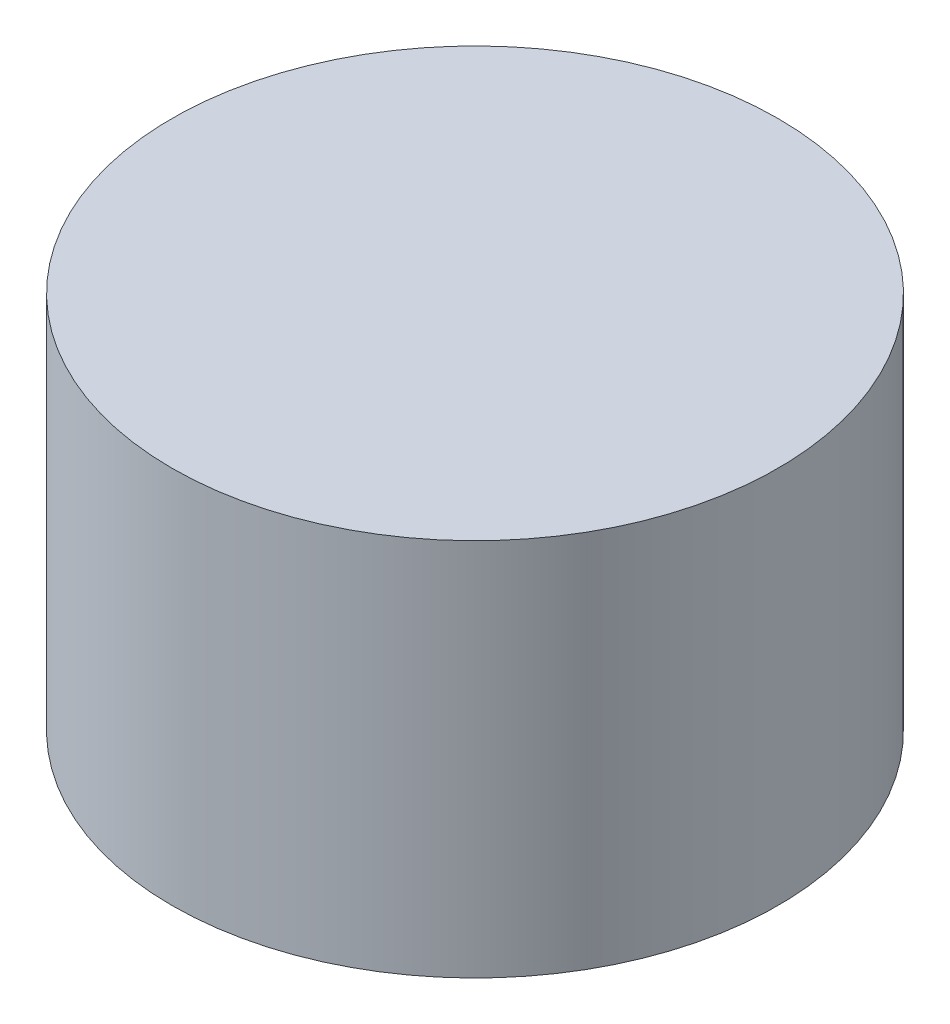
SolidWorks part; units mm, degrees
ref_plane "Front Plane" through (0, 0, 0) normal (0, 0, 1) x (1, 0, 0)
ref_plane "Top Plane" through (0, 0, 0) normal (0, 1, 0) x (1, 0, 0)
ref_plane "Right Plane" through (0, 0, 0) normal (1, 0, 0) x (0, 0, -1)
sketch "Sketch1" plane through (0, 0, 0) normal (0, 1, 0) x (1, 0, 0)
  circle A0 centre (0, 0) radius 6.35
  dimension "D1" = 12.7
extrude "Boss-Extrude1" add sketch "Sketch1" along normal blind 7.9375
